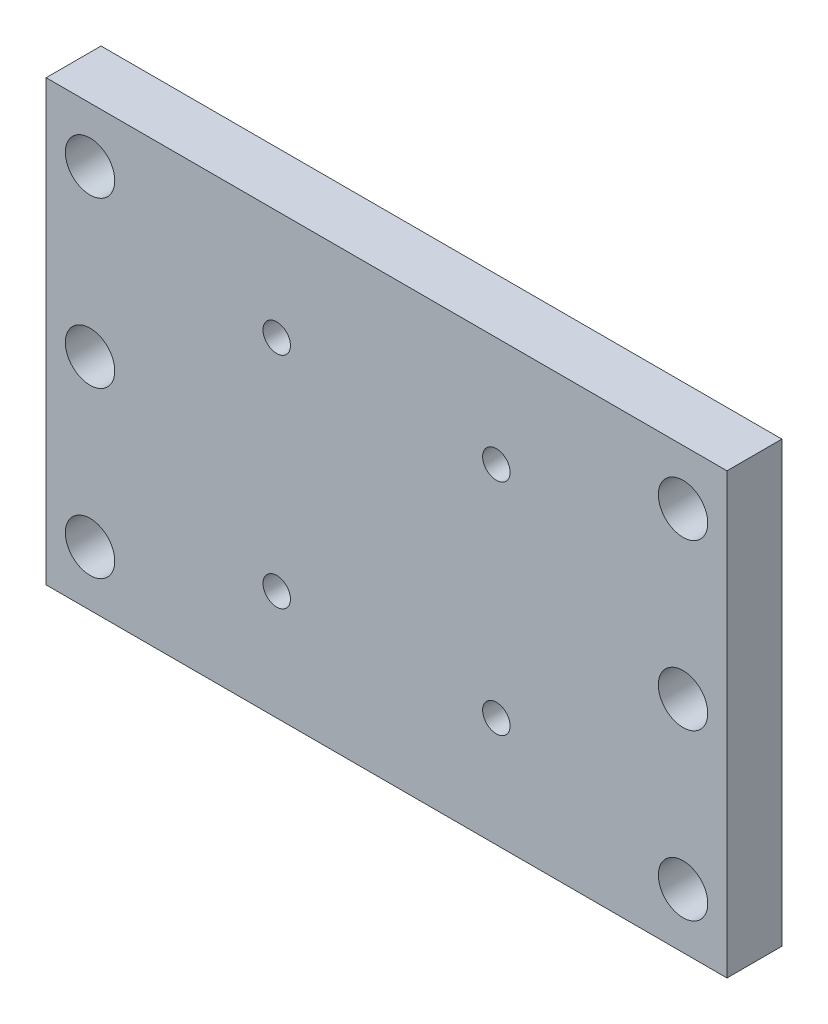
SolidWorks part; units mm, degrees
ref_plane "Ebene vorne" through (0, 0, 0) normal (0, 0, 1) x (1, 0, 0)
ref_plane "Ebene oben" through (0, 0, 0) normal (0, 1, 0) x (1, 0, 0)
ref_plane "Ebene rechts" through (0, 0, 0) normal (1, 0, 0) x (0, 0, -1)
sketch "Skizze1" plane through (0, 0, 0) normal (0, 0, 1) x (1, 0, 0)
  line L0 (0, 0) -> (0, 13.409) construction
  line L1 (-31, 15.4004) -> (31, 15.4004)
  line L2 (-31, 15.4004) -> (-31, -24.5996)
  line L3 (-31, -24.5996) -> (31, -24.5996)
  line L4 (31, 15.4004) -> (31, -24.5996)
  line L5 (-31, -4.5996) -> (31, -4.5996) construction
  line L6 (-10, 5.4004) -> (-10, -14.5996) construction
  line L7 (10, 5.4004) -> (10, -14.5996) construction
  circle A0 centre (-27, 10.4004) radius 2.25
  circle A1 centre (-27, -4.5996) radius 2.25
  circle A2 centre (-27, -19.5996) radius 2.25
  circle A3 centre (-10, 5.4004) radius 1.25
  circle A4 centre (-10, -14.5996) radius 1.25
  circle A5 centre (10, 5.4004) radius 1.25
  circle A6 centre (10, -14.5996) radius 1.25
  circle A7 centre (27, -19.5996) radius 2.25
  circle A8 centre (27, -4.5996) radius 2.25
  circle A9 centre (27, 10.4004) radius 2.25
  dimension "D9" = 4.5
  dimension "D10" = 4.5
  dimension "D11" = 4.5
  dimension "D16" = 2.5
  dimension "D17" = 2.5
  dimension "D1" = 62
  dimension "D2" = 31
  dimension "D3" = 15
  dimension "D4" = 15
  dimension "D5" = 40
  dimension "D6" = 27
  dimension "D7" = 27
  dimension "D8" = 27
  dimension "D12" = 10
  dimension "D13" = 10
  dimension "D14" = 20
  dimension "D15" = 20
extrude "Aufsatz-Linear austragen1" add sketch "Skizze1" along normal blind 5
